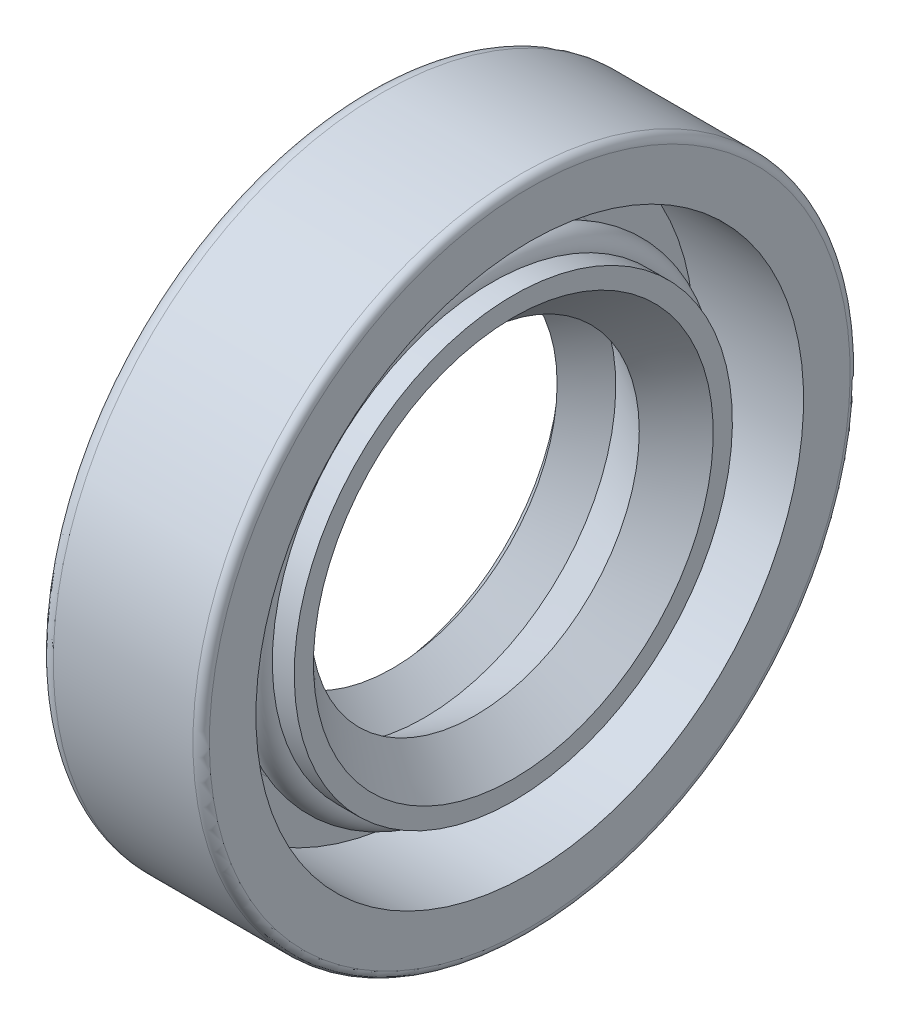
SolidWorks part; units mm, degrees
ref_plane "Front" through (0, 0, 0) normal (0, 0, 1) x (1, 0, 0)
ref_plane "Top" through (0, 0, 0) normal (0, 1, 0) x (1, 0, 0)
ref_plane "Right" through (0, 0, 0) normal (1, 0, 0) x (0, 0, -1)
sketch "Sketch1" plane through (0, 0, 0) normal (0, 0, 1) x (1, 0, 0)
  line L0 (0, 10.5833) -> (0.1984, 10.5833)
  line L1 (0.1984, 10.5833) -> (0.1984, 8.4667)
  line L2 (0.1984, 8.4667) -> (0, 8.4667)
  line L3 (0, 8.4667) -> (0, 7.9375)
  line L4 (0, 7.9375) -> (1.0583, 7.4083)
  line L5 (1.0583, 7.4083) -> (0.5338, 6.9488)
  line L6 (0.5338, 6.9488) -> (1.0583, 6.35)
  line L7 (1.0583, 6.35) -> (2.2665, 7.4083)
  line L8 (2.2665, 7.4083) -> (4.2333, 6.35)
  line L9 (4.2333, 6.35) -> (5.715, 7.7258)
  line L10 (5.715, 7.7258) -> (5.715, 8.4667)
  line L11 (5.715, 8.4667) -> (4.8683, 8.4667)
  line L12 (3.5983, 8.4667) -> (2.4342, 8.4667)
  line L13 (2.1167, 8.7842) -> (2.1167, 10.5833)
  line L14 (2.1167, 10.5833) -> (6.35, 10.5833)
  line L15 (6.35, 10.5833) -> (6.35, 12.3825)
  line L16 (6.0325, 12.7) -> (0.635, 12.7)
  line L17 (0, 12.065) -> (0, 10.5833)
  line L18 (6.35, 0) -> (0, 0) construction
  line L19 (1.0583, 6.35) -> (4.2333, 6.35) construction
  line L20 (3.3337, 12.7) -> (3.3337, 10.5833) construction
  line L21 (3.3337, 10.5833) -> (3.3337, 8.4667) construction
  line L22 (3.3337, 8.4667) -> (3.3337, 6.35) construction
  line L23 (4.2333, 8.4667) -> (4.2333, 6.35) construction
  line L24 (0, 11.3242) -> (2.1167, 11.3242) construction
  line L25 (2.1167, 11.3242) -> (4.2333, 11.3242) construction
  line L26 (4.2333, 11.3242) -> (6.35, 11.3242) construction
  line L27 (4.2333, 8.4667) -> (4.2333, 11.3242) construction
  line L28 (2.1167, 8.7842) -> (2.2665, 7.4083) construction
  line L29 (3.3337, 7.4083) -> (2.2665, 7.4083) construction
  line L30 (2.8001, 7.4083) -> (2.8001, 8.4667) construction
  line L31 (2.8001, 7.9375) -> (0, 7.9375) construction
  line L32 (2.2665, 7.4083) -> (1.0583, 7.4083) construction
  line L33 (1.0583, 6.35) -> (1.0583, 7.4083) construction
  line L35 (6.35, 10.5833) -> (6.35, 8.4667) construction
  line L36 (6.35, 8.4667) -> (5.715, 8.4667) construction
  line L37 (0, 12.065) -> (0.635, 12.065) construction
  line L39 (1.0583, 11.3242) -> (1.0583, 7.4083) construction
  arc A0 (4.8683, 8.4667) -> (3.5983, 8.4667) centre (4.2333, 8.4667) ccw construction
  arc A1 (2.4342, 8.4667) -> (2.1167, 8.7842) centre (2.4342, 8.7842) cw
  arc A2 (6.35, 12.3825) -> (6.0325, 12.7) centre (6.0325, 12.3825) ccw
  arc A3 (0.635, 12.7) -> (0, 12.065) centre (0.635, 12.065) ccw
  arc A4 (3.5983, 8.4667) -> (4.8683, 8.4667) centre (4.2333, 8.4667) ccw
  dimension "D3" = 0.635
  dimension "D4" = 0.3175
  dimension "D2" = 0.1984
  dimension "D5" = 67.784
  dimension "D8" = 47.121
revolve "Revolve1" add sketch "Sketch1" angle 360 about L18
sketch "Sketch2" plane through (0, 0, 0) normal (0, 0, 1) x (1, 0, 0)
  line L0 (0, 0) -> (6.35, 0) construction
  circle A0 centre (4.2333, 8.4667) radius 0.635
revolve "Revolve2" add sketch "Sketch2" angle 360 about L0
equation "\"D2@Sketch1\"=\"SealWidth@Sketch1\"*.03125"
equation "\"D3@Sketch1\"=\"SealWidth@Sketch1\"*.1"
equation "\"D4@Sketch1\"=\"D3@Sketch1\"*.5"
